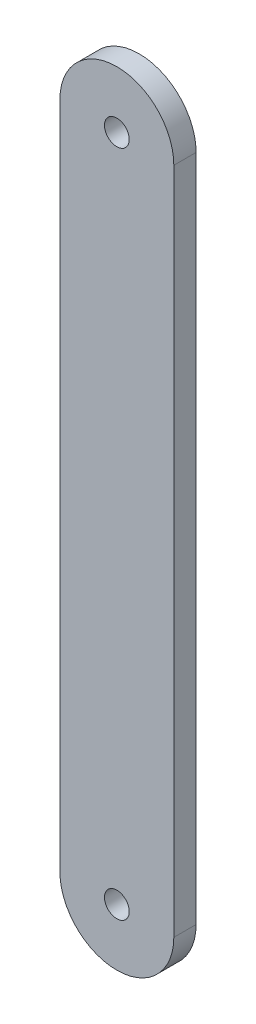
SolidWorks part; units mm, degrees
ref_plane "Front Plane" through (0, 0, 0) normal (0, 0, 1) x (1, 0, 0)
ref_plane "Top Plane" through (0, 0, 0) normal (0, 1, 0) x (1, 0, 0)
ref_plane "Right Plane" through (0, 0, 0) normal (1, 0, 0) x (0, 0, -1)
sketch "Sketch1" plane through (0, 0, 0) normal (0, 0, 1) x (1, 0, 0)
  line L0 (-12.78, 150) -> (-12.78, 0)
  line L1 (12.78, 0) -> (12.78, 150)
  circle A0 centre (0, 0) radius 2.78
  circle A1 centre (0, 0) radius 12.78
  circle A2 centre (0, 150) radius 2.78
  circle A3 centre (0, 150) radius 12.78
  dimension "D1" = 5.56
  dimension "D3" = 5.56
  dimension "D4" = 150
  dimension "D2" = 10
  dimension "D5" = 10
extrude "Boss-Extrude1" add sketch "Sketch1" along normal mid plane 5 contours A3 L0 A1 L1 | A3 A2 | A1 A0
